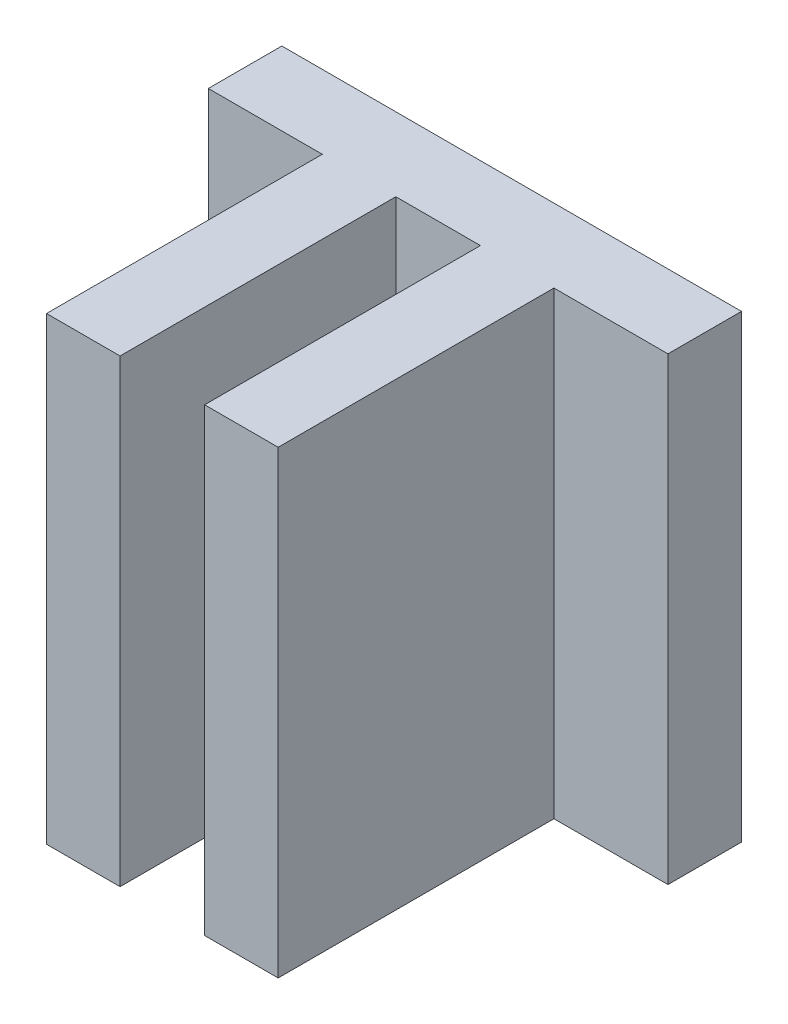
SolidWorks part; units mm, degrees
ref_plane "Front Plane" through (0, 0, 0) normal (0, 0, 1) x (1, 0, 0)
ref_plane "Top Plane" through (0, 0, 0) normal (0, 1, 0) x (1, 0, 0)
ref_plane "Right Plane" through (0, 0, 0) normal (1, 0, 0) x (0, 0, -1)
sketch "Sketch1" plane through (0, 0, 0) normal (0, 1, 0) x (1, 0, 0)
  line L1 (-4.0005, 2.54) -> (4.0005, 2.54)
  line L2 (-4.0005, 2.54) -> (-4.0005, -9.525)
  line L3 (-4.0005, -9.525) -> (4.0005, -9.525)
  line L4 (4.0005, 2.54) -> (4.0005, -9.525)
  line L5 (-1.4605, -9.525) -> (1.4605, -9.525) construction
  line L6 (-1.4605, -9.525) -> (-1.4605, 0)
  line L7 (-1.4605, 0) -> (1.4605, 0)
  line L8 (1.4605, -9.525) -> (1.4605, 0)
  line L9 (-4.0005, 0) -> (-7.9375, 0)
  line L10 (-4.0005, 0) -> (-4.0005, 2.54)
  line L11 (-4.0005, 2.54) -> (-7.9375, 2.54)
  line L12 (-7.9375, 0) -> (-7.9375, 2.54)
  line L13 (4.0005, 0) -> (7.9375, 0)
  line L14 (4.0005, 0) -> (4.0005, 2.54)
  line L15 (4.0005, 2.54) -> (7.9375, 2.54)
  line L16 (7.9375, 0) -> (7.9375, 2.54)
  point P8 (0, 0)
  point P10 (0, 2.54)
  dimension "D1" = 2.921
  dimension "D2" = 2.54
  dimension "D3" = 9.525
  dimension "D4" = 2.54
  dimension "D5" = 15.875
extrude "Boss-Extrude1" add sketch "Sketch1" along normal blind 15.875 contours L8 L3 L4 L1 L2 L6 L7 | L12 L9 L2 L11 | L13 L16 L15 L4
